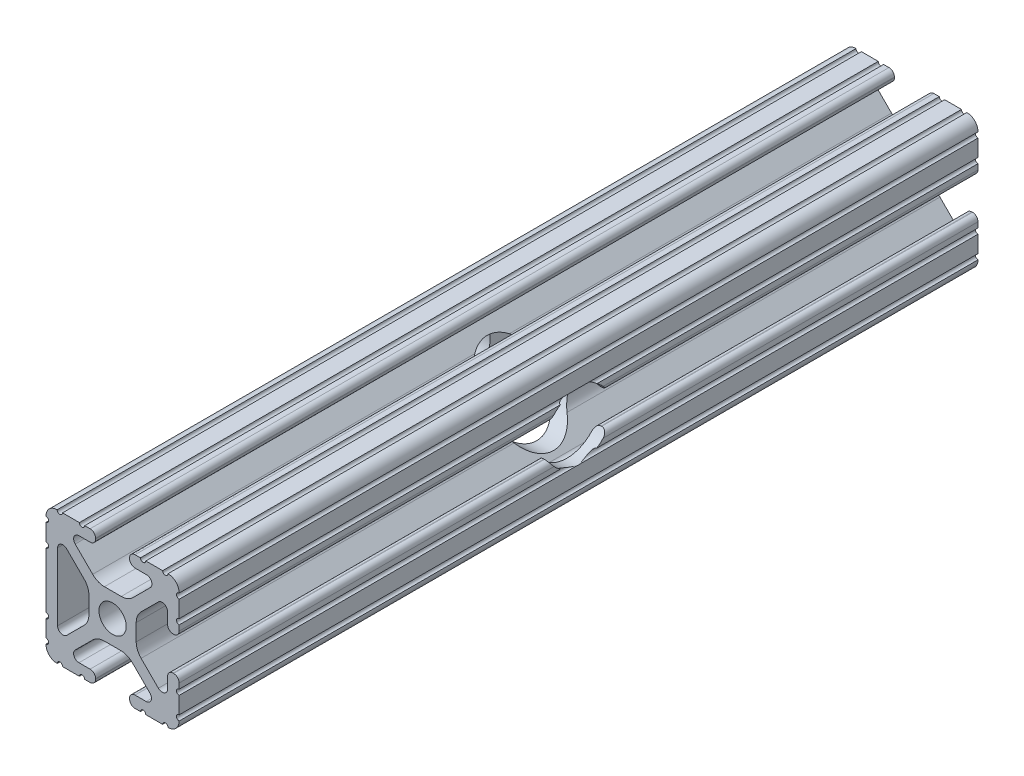
SolidWorks part; units mm, degrees
material "6061-T6 (SS)"
ref_plane "Front Plane" through (0, 0, 0) normal (0, 0, 1) x (1, 0, 0)
ref_plane "Top Plane" through (0, 0, 0) normal (0, 1, 0) x (1, 0, 0)
ref_plane "Right Plane" through (0, 0, 0) normal (1, 0, 0) x (0, 0, -1)
ref_plane "Plane1" through (0, 0, -152.4) normal (0, 0, -1) x (-1, 0, 0)
sketch "Sketch1" plane through (0, 0, -152.4) normal (0, 0, -1) x (-1, 0, 0)
  line L0 (6.4164, -10.4902) -> (4.2875, -10.4902)
  line L1 (3.2385, -11.5392) -> (3.2385, -11.651)
  line L2 (4.2875, -12.7) -> (5.3171, -12.7)
  line L3 (6.3331, -12.7) -> (9.5504, -12.7)
  line L4 (12.7, -9.5504) -> (12.7, -6.3331)
  line L5 (12.7, -5.3171) -> (12.7, 5.3171)
  line L6 (12.7, 6.3331) -> (12.7, 9.5504)
  line L7 (9.5504, 12.7) -> (6.3331, 12.7)
  line L8 (5.3171, 12.7) -> (4.2875, 12.7)
  line L9 (3.2384, 11.651) -> (3.2384, 11.5392)
  line L10 (4.2875, 10.4902) -> (6.4164, 10.4902)
  line L11 (7.1341, 8.7551) -> (3.7966, 5.4237)
  line L12 (1.5536, 4.4958) -> (-1.6573, 4.4958)
  line L13 (-3.9003, 5.4237) -> (-7.2072, 8.7245)
  line L14 (-6.4768, 10.4902) -> (-4.2875, 10.4902)
  line L15 (-3.2384, 11.5392) -> (-3.2384, 11.651)
  line L16 (-4.2875, 12.7) -> (-5.3171, 12.7)
  line L17 (-6.3331, 12.7) -> (-9.5504, 12.7)
  line L18 (-12.7, 9.5504) -> (-12.7, 6.3331)
  line L19 (-12.7, 5.3171) -> (-12.7, 4.2875)
  line L20 (-11.651, 3.2385) -> (-11.5392, 3.2385)
  line L21 (-10.4902, 4.2875) -> (-10.4902, 6.4021)
  line L22 (-8.737, 7.1292) -> (-5.4405, 3.8388)
  line L23 (-4.5085, 1.5917) -> (-4.5085, -1.5917)
  line L24 (-5.4405, -3.8388) -> (-8.737, -7.1292)
  line L25 (-10.4902, -6.4021) -> (-10.4902, -4.2875)
  line L26 (-11.5392, -3.2385) -> (-11.651, -3.2385)
  line L27 (-12.7, -4.2875) -> (-12.7, -5.3171)
  line L28 (-12.7, -6.3331) -> (-12.7, -9.5504)
  line L29 (-9.5504, -12.7) -> (-6.3331, -12.7)
  line L30 (-5.3171, -12.7) -> (-4.2875, -12.7)
  line L31 (-3.2385, -11.651) -> (-3.2385, -11.5392)
  line L32 (-4.2875, -10.4902) -> (-6.4083, -10.4902)
  line L33 (-7.1285, -8.7494) -> (-3.7967, -5.4237)
  line L34 (-1.5536, -4.4958) -> (1.5536, -4.4958)
  line L35 (3.7967, -5.4237) -> (7.1342, -8.7551)
  line L36 (10.4902, 6.4464) -> (10.4902, -6.4254)
  line L37 (8.7534, -7.1457) -> (5.4405, -3.8388)
  line L38 (4.5085, -1.5917) -> (4.5085, 1.5917)
  line L39 (5.4405, 3.8388) -> (8.7683, 7.1606)
  arc A0 (4.2875, -10.4902) -> (3.2385, -11.5392) centre (4.2875, -11.5392) ccw
  arc A1 (3.2385, -11.651) -> (4.2875, -12.7) centre (4.2875, -11.651) ccw
  arc A2 (5.3171, -12.7) -> (6.3331, -12.7) centre (5.8251, -12.7) cw
  arc A3 (9.5504, -12.7) -> (10.5664, -12.6998) centre (10.0584, -12.7) cw
  arc A4 (10.5664, -12.6998) -> (12.6998, -10.5664) centre (10.5918, -10.5918) ccw
  arc A5 (12.6998, -10.5664) -> (12.7, -9.5504) centre (12.7, -10.0584) cw
  arc A6 (12.7, -6.3331) -> (12.7, -5.3171) centre (12.7, -5.8251) cw
  arc A7 (12.7, 5.3171) -> (12.7, 6.3331) centre (12.7, 5.8251) cw
  arc A8 (12.7, 9.5504) -> (12.6998, 10.5664) centre (12.7, 10.0584) cw
  arc A9 (12.6998, 10.5664) -> (10.5664, 12.6998) centre (10.5918, 10.5918) ccw
  arc A10 (10.5664, 12.6998) -> (9.5504, 12.7) centre (10.0584, 12.7) cw
  arc A11 (6.3331, 12.7) -> (5.3171, 12.7) centre (5.8251, 12.7) cw
  arc A12 (4.2875, 12.7) -> (3.2384, 11.651) centre (4.2875, 11.651) ccw
  arc A13 (3.2384, 11.5392) -> (4.2875, 10.4902) centre (4.2875, 11.5392) ccw
  arc A14 (6.4164, 10.4902) -> (7.1341, 8.7551) centre (6.4164, 9.4742) cw
  arc A15 (3.7966, 5.4237) -> (1.5536, 4.4958) centre (1.5536, 7.6708) cw
  arc A16 (-1.6573, 4.4958) -> (-3.9003, 5.4237) centre (-1.6573, 7.6708) cw
  arc A17 (-7.2072, 8.7245) -> (-6.4768, 10.4902) centre (-6.4768, 9.4563) cw
  arc A18 (-4.2875, 10.4902) -> (-3.2384, 11.5392) centre (-4.2875, 11.5392) ccw
  arc A19 (-3.2384, 11.651) -> (-4.2875, 12.7) centre (-4.2875, 11.651) ccw
  arc A20 (-5.3171, 12.7) -> (-6.3331, 12.7) centre (-5.8251, 12.7) cw
  arc A21 (-9.5504, 12.7) -> (-10.5664, 12.6998) centre (-10.0584, 12.7) cw
  arc A22 (-10.5664, 12.6998) -> (-12.6998, 10.5664) centre (-10.5918, 10.5918) ccw
  arc A23 (-12.6998, 10.5664) -> (-12.7, 9.5504) centre (-12.7, 10.0584) cw
  arc A24 (-12.7, 6.3331) -> (-12.7, 5.3171) centre (-12.7, 5.8251) cw
  arc A25 (-12.7, 4.2875) -> (-11.651, 3.2385) centre (-11.651, 4.2875) ccw
  arc A26 (-11.5392, 3.2385) -> (-10.4902, 4.2875) centre (-11.5392, 4.2875) ccw
  arc A27 (-10.4902, 6.4021) -> (-8.737, 7.1292) centre (-9.4628, 6.4021) cw
  arc A28 (-5.4405, 3.8388) -> (-4.5085, 1.5917) centre (-7.6835, 1.5917) cw
  arc A29 (-4.5085, -1.5917) -> (-5.4405, -3.8388) centre (-7.6835, -1.5917) cw
  arc A30 (-8.737, -7.1292) -> (-10.4902, -6.4021) centre (-9.4628, -6.4021) cw
  arc A31 (-10.4902, -4.2875) -> (-11.5392, -3.2385) centre (-11.5392, -4.2875) ccw
  arc A32 (-11.651, -3.2385) -> (-12.7, -4.2875) centre (-11.651, -4.2875) ccw
  arc A33 (-12.7, -5.3171) -> (-12.7, -6.3331) centre (-12.7, -5.8251) cw
  arc A34 (-12.7, -9.5504) -> (-12.6998, -10.5664) centre (-12.7, -10.0584) cw
  arc A35 (-12.6998, -10.5664) -> (-10.5664, -12.6998) centre (-10.5918, -10.5918) ccw
  arc A36 (-10.5664, -12.6998) -> (-9.5504, -12.7) centre (-10.0584, -12.7) cw
  arc A37 (-6.3331, -12.7) -> (-5.3171, -12.7) centre (-5.8251, -12.7) cw
  arc A38 (-4.2875, -12.7) -> (-3.2385, -11.651) centre (-4.2875, -11.651) ccw
  arc A39 (-3.2385, -11.5392) -> (-4.2875, -10.4902) centre (-4.2875, -11.5392) ccw
  arc A40 (-6.4083, -10.4902) -> (-7.1285, -8.7494) centre (-6.4083, -9.4709) cw
  arc A41 (-3.7967, -5.4237) -> (-1.5536, -4.4958) centre (-1.5536, -7.6708) cw
  arc A42 (1.5536, -4.4958) -> (3.7967, -5.4237) centre (1.5536, -7.6708) cw
  arc A43 (7.1342, -8.7551) -> (6.4164, -10.4902) centre (6.4164, -9.4742) cw
  arc A44 (8.7683, 7.1606) -> (10.4902, 6.4464) centre (9.4812, 6.4464) cw
  arc A45 (10.4902, -6.4254) -> (8.7534, -7.1457) centre (9.4724, -6.4254) cw
  arc A46 (5.4405, -3.8388) -> (4.5085, -1.5917) centre (7.6835, -1.5917) cw
  arc A47 (4.5085, 1.5917) -> (5.4405, 3.8388) centre (7.6835, 1.5917) cw
  circle A48 centre (0, 0) radius 2.6035
extrude "Boss-Extrude1" add sketch "Sketch1" against normal blind 152.4
sketch "Sketch2" plane through (-12.7, 0, 0) normal (-1, 0, 0) x (0, 0, 1)
  line L4 (-152.4, -5.3171) -> (-152.4, 5.3171) construction
  circle A0 centre (-76.2, 0) radius 6.35
  dimension "D1" = 76.2
extrude "Cut-Extrude1" cut sketch "Sketch2" against normal through all
